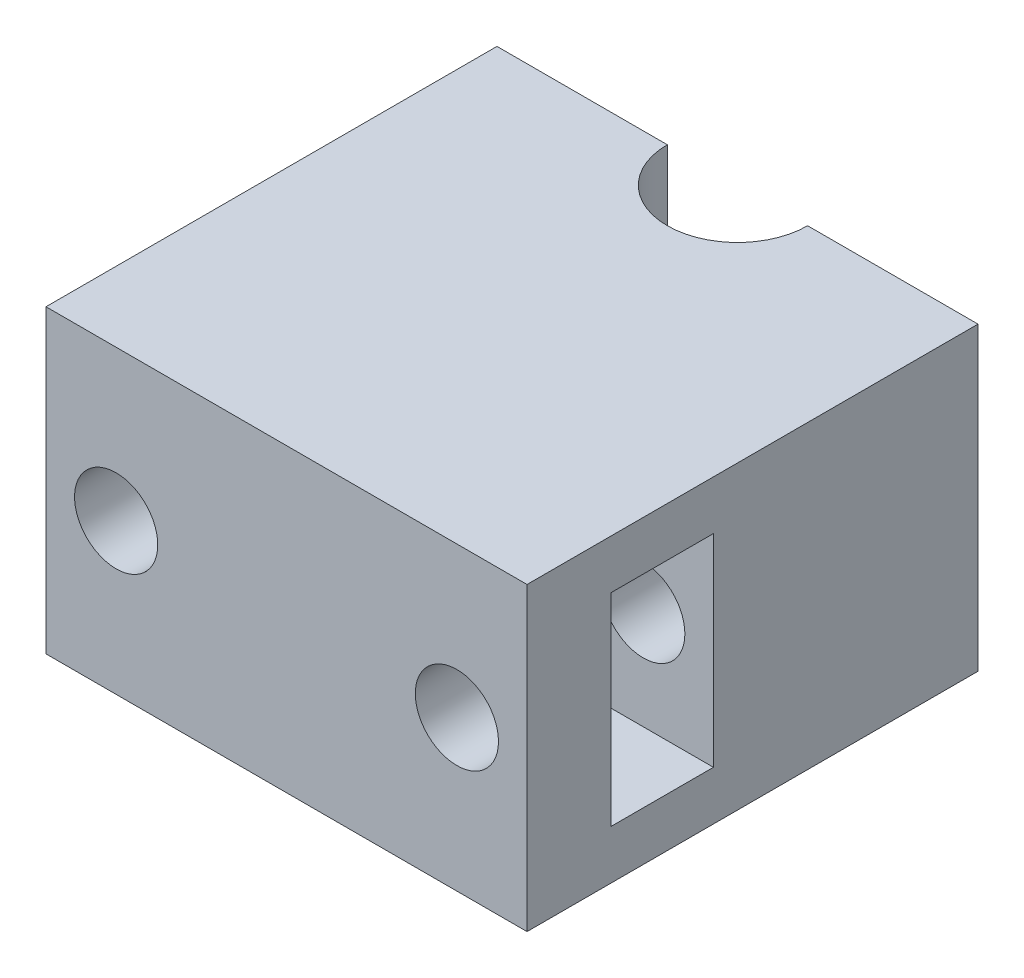
SolidWorks part; units mm, degrees
ref_plane "Спереди" through (0, 0, 0) normal (0, 0, 1) x (1, 0, 0)
ref_plane "Сверху" through (0, 0, 0) normal (0, 1, 0) x (1, 0, 0)
ref_plane "Справа" through (0, 0, 0) normal (1, 0, 0) x (0, 0, -1)
sketch "Sketch1" plane through (0, 0, 0) normal (0, 1, 0) x (1, 0, 0)
  line L1 (24, -22.5) -> (-24, -22.5)
  line L2 (24, -22.5) -> (24, 22.5)
  line L3 (24, 22.5) -> (-24, 22.5)
  line L4 (-24, -22.5) -> (-24, 22.5)
  line L5 (24, -22.5) -> (-24, 22.5) construction
  line L6 (24, 22.5) -> (-24, -22.5) construction
  point P0 (0, 0)
  dimension "D1" = 48
  dimension "D2" = 45
extrude "Boss-Extrude1" add sketch "Sketch1" along normal blind 30
sketch "Sketch2" plane through (24, 0, 0) normal (1, 0, 0) x (0, 0, -1)
  line L0 (-22.5, 15) -> (22.5, 15) construction
  line L1 (-22.5, 30) -> (-22.5, 0) construction
  line L2 (22.5, 30) -> (22.5, 0) construction
  line L4 (-14.1, 4.9) -> (-3.9, 4.9)
  line L5 (-14.1, 4.9) -> (-14.1, 25.1)
  line L6 (-14.1, 25.1) -> (-3.9, 25.1)
  line L7 (-3.9, 4.9) -> (-3.9, 25.1)
  line L8 (-14.1, 4.9) -> (-3.9, 25.1) construction
  line L9 (-14.1, 25.1) -> (-3.9, 4.9) construction
  point P6 (-9, 15)
  dimension "D1" = 10.2
  dimension "D2" = 20.2
  dimension "D3" = 31.5
extrude "Cut-Extrude1" cut sketch "Sketch2" against normal offset from surface (45 mm away) 3 up to face at (-24, 15, 0)
sketch "Sketch3" plane through (0, 0, 22.5) normal (0, 0, 1) x (1, 0, 0)
  line L0 (-24, 15) -> (24, 15) construction
  line L1 (-24, 30) -> (-24, 0) construction
  line L2 (24, 30) -> (24, 0) construction
  circle A0 centre (-17, 15) radius 4.15
  circle A1 centre (17, 15) radius 4.15
  point P10 (0, 15)
  dimension "D1" = 34
  dimension "D2" = 8.3
  dimension "D3" = 17
extrude "Cut-Extrude2" cut sketch "Sketch3" against normal through all
sketch "Sketch4" plane through (0, 30, 0) normal (0, 1, 0) x (1, 0, 0)
  line L0 (0, 22.5) -> (0, -22.5) construction
  line L1 (24, 22.5) -> (-24, 22.5) construction
  line L2 (-24, -22.5) -> (24, -22.5) construction
  arc A0 (-7, 22.5) -> (7, 22.5) centre (0, 22.5) ccw
  dimension "D1" = 7
extrude "Cut-Extrude3" cut sketch "Sketch4" against normal through all and the other way through all
